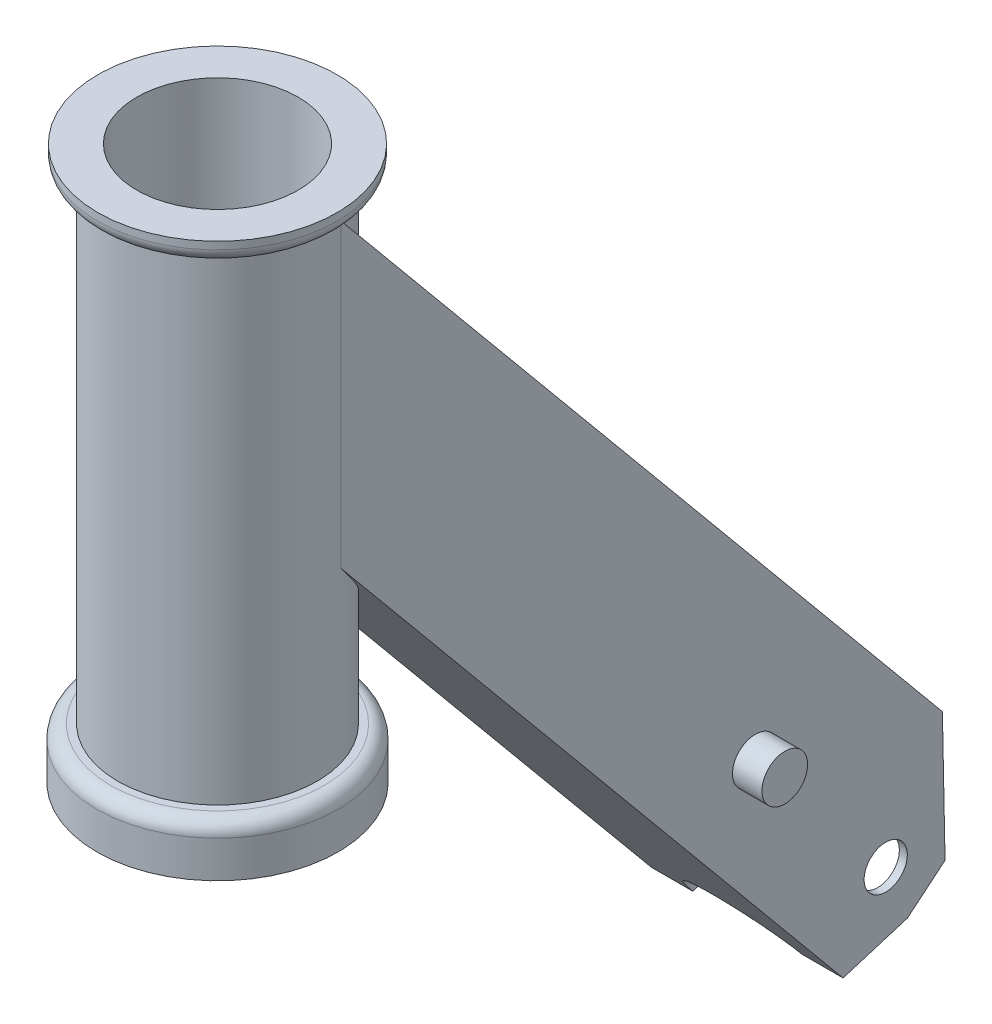
SolidWorks part; units mm, degrees
ref_plane "Front Plane" through (0, 0, 0) normal (0, 0, 1) x (1, 0, 0)
ref_plane "Top Plane" through (0, 0, 0) normal (0, 1, 0) x (1, 0, 0)
ref_plane "Right Plane" through (0, 0, 0) normal (1, 0, 0) x (0, 0, -1)
sketch "Sketch3" plane through (0, 0, 0) normal (0, 0, 1) x (1, 0, 0)
  line L0 (0, 0) -> (22.1742, 0)
  line L1 (22.1742, 0) -> (22.1742, 6.7818)
  line L2 (19.6342, 9.3218) -> (18.3134, 9.3218)
  line L3 (18.3134, 9.3218) -> (18.3134, 97.6884)
  line L4 (18.3134, 97.6884) -> (19.431, 97.6884)
  line L5 (21.971, 100.2284) -> (21.971, 101.6)
  line L6 (21.971, 101.6) -> (0, 101.6)
  line L7 (0, 101.6) -> (0, 0)
  arc A0 (22.1742, 6.7818) -> (19.6342, 9.3218) centre (19.6342, 6.7818) ccw
  arc A1 (19.431, 97.6884) -> (21.971, 100.2284) centre (19.431, 100.2284) ccw
  point P13 (21.971, 97.6884)
  dimension "D3" = 2.54
  dimension "D8" = 2.54
  dimension "D1" = 22.1742
  dimension "D2" = 9.3218
  dimension "D4" = 18.3134
  dimension "D5" = 21.971
  dimension "D6" = 101.6
  dimension "D7" = 3.9116
revolve "Revolve1" add sketch "Sketch3" angle 360 about L7
sketch "Sketch4" plane through (0, 0, 0) normal (1, 0, 0) x (0, 0, -1)
  line L0 (3.3197, 97.6884) -> (115.5728, -37.7445)
  line L1 (0, 46.4272) -> (97.331, -71.0024)
  line L2 (18.3197, 79.5909) -> (0, 79.5909) construction
  line L3 (21.971, 101.6) -> (-21.971, 101.6) construction
  line L4 (0, 0) -> (38.481, 0) construction
  line L5 (-22.1742, 0) -> (22.1742, 0) construction
  line L6 (-18.3134, 97.6884) -> (18.3134, 97.6884) construction
  line L7 (3.3197, 97.6884) -> (0, 46.4272)
  line L8 (115.5728, -37.7445) -> (116.0589, -61.6556)
  line L9 (116.0589, -61.6556) -> (109.1362, -67.3936)
  line L10 (109.1362, -67.3936) -> (97.331, -71.0024)
  circle A0 centre (105.1571, -57.2891) radius 3.9688
  dimension "D10" = 7.9375
  dimension "D1" = 35.2679
  dimension "D2" = 18.3197
  dimension "D3" = 22.0091
  dimension "D4" = 38.481
  dimension "D5" = 152.4
  dimension "D6" = 18.7198
  dimension "D7" = 14.8844
  dimension "D8" = 8.9916
  dimension "D9" = 12.3444
  dimension "D11" = 14.7765
  dimension "D12" = 10.3187
extrude "Boss-Extrude1" add sketch "Sketch4" along normal mid plane 35.179
sketch "Sketch5" plane through (0, -93.5696, -77.5548) normal (0, -0.7699, -0.6381) x (1, 0, 0)
  line L0 (17.5895, -29.6272) -> (-17.5895, -29.6272) construction
  line L1 (-16.129, -63.4346) -> (16.129, -63.4346)
  line L2 (-16.129, -63.4346) -> (-16.129, -31.0877)
  line L3 (-16.129, -31.0877) -> (16.129, -31.0877)
  line L4 (16.129, -63.4346) -> (16.129, -31.0877)
  line L5 (17.5895, -29.6272) -> (17.5895, -41.0191) construction
  line L6 (-17.5895, -29.6272) -> (-17.5895, -41.0191) construction
  line L7 (-17.5895, -64.8951) -> (17.5895, -64.8951) construction
  point P8 (-17.5895, -35.3231)
  dimension "D1" = 1.4605
  dimension "D2" = 1.4605
  dimension "D3" = 1.4605
  dimension "D4" = 1.4605
extrude "Cut-Extrude1" cut sketch "Sketch5" against normal blind 149.479
sketch "Sketch6" plane through (0, 41.4124, -49.9639) normal (0, 0.6381, -0.7699) x (-1, 0, 0)
  line L1 (14.9225, -97.7449) -> (14.9225, -112.9074)
  line L2 (14.9225, -112.9074) -> (-14.9225, -112.9074)
  line L3 (-14.9225, -112.9074) -> (-14.9225, -97.7449)
  line L4 (-17.5895, -102.8122) -> (17.5895, -102.8122) construction
  arc A0 (-14.9225, -97.7449) -> (14.9225, -97.7449) centre (0, -97.7449) cw
  point P7 (0, -102.8122)
  dimension "D1" = 14.9225
  dimension "D2" = 5.0673
extrude "Cut-Extrude2" cut sketch "Sketch6" against normal up to next
sketch "Sketch7" plane through (0, 18.9064, -22.8105) normal (0, -0.6381, 0.7699) x (1, 0, 0)
  line L0 (17.5895, -116.7771) -> (-17.5895, -116.7771) construction
  line L1 (-9.989, -117.3867) -> (9.989, -117.3867)
  line L2 (-16.129, -117.3867) -> (16.129, -117.3867) construction
  arc A0 (-9.989, -117.3867) -> (9.989, -117.3867) centre (0, -116.7771) cw
  dimension "D1" = 10.0076
extrude "Cut-Extrude3" cut sketch "Sketch7" against normal up to next
sketch "Sketch8" plane through (17.5895, 0, 0) normal (1, 0, 0) x (0, 0, -1)
  line L1 (109.1362, -67.3936) -> (116.0589, -61.6556) construction
  line L2 (5.098, 40.2764) -> (97.331, -71.0024) construction
  circle A0 centre (81.207, -28.3636) radius 4.1974
  dimension "D2" = 8.3947
  dimension "D1" = 47.8726
  dimension "D3" = 14.7955
extrude "Boss-Extrude2" add sketch "Sketch8" along normal blind 5.4102
mirror "Mirror1" about plane through (0, 0, 0) normal (1, 0, 0) of "Boss-Extrude2"
sketch "Sketch9" plane through (0, 0, 0) normal (0, -1, 0) x (1, 0, 0)
  circle A0 centre (0, 0) radius 14.8209
  dimension "D1" = 29.6418
extrude "Cut-Extrude4" cut sketch "Sketch9" against normal through all
